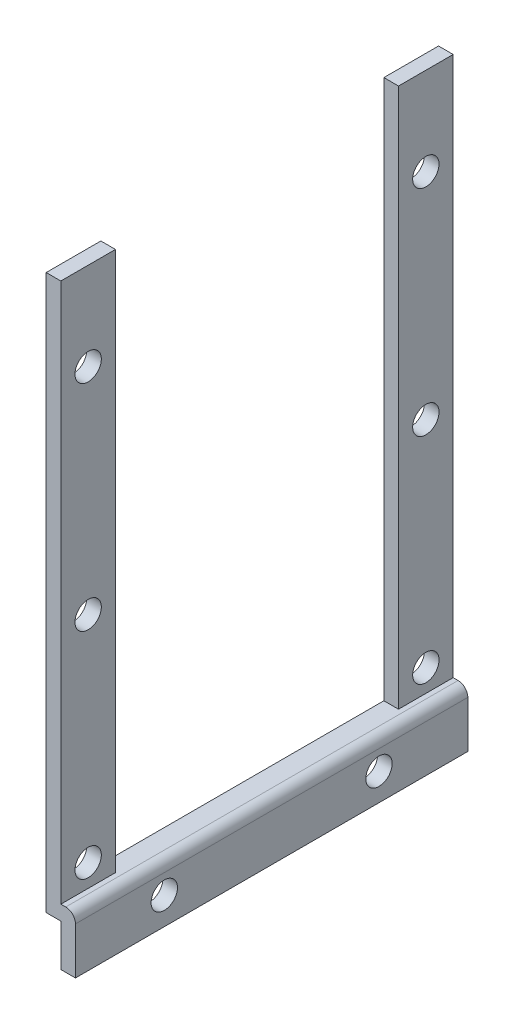
SolidWorks part; units mm, degrees
material "ABS"
ref_plane "Front Plane" through (0, 0, 0) normal (0, 0, 1) x (1, 0, 0)
ref_plane "Top Plane" through (0, 0, 0) normal (0, 1, 0) x (1, 0, 0)
ref_plane "Right Plane" through (0, 0, 0) normal (1, 0, 0) x (0, 0, -1)
sketch "Sketch1" plane through (0, 0, 0) normal (0, 0, 1) x (1, 0, 0)
  line L0 (0, 0) -> (0, 4.3)
  line L1 (0, 4.3) -> (-1.5, 4.3)
  line L2 (-1.5, 4.3) -> (-1.5, 61.1)
  line L3 (-1.5, 61.1) -> (0, 61.1)
  line L4 (0, 61.1) -> (0, 5.8)
  line L5 (0, 5.8) -> (1.5, 5.8)
  line L6 (1.5, 5.8) -> (1.5, 0)
  line L7 (1.5, 0) -> (0, 0)
  dimension "D1" = 1.5
  dimension "D2" = 1.5
  dimension "D3" = 1.5
  dimension "D4" = 61.1
  dimension "D5" = 4.3
  dimension "D6" = 1.5
extrude "Boss-Extrude1" add sketch "Sketch1" against normal blind 40.2
sketch "Sketch3" plane through (0, 0, 0) normal (1, 0, 0) x (0, 0, -1)
  line L0 (40.2, 61.1) -> (0, 61.1) construction
  line L1 (5.6, 61.1) -> (34.6, 61.1)
  line L2 (5.6, 61.1) -> (5.6, 5.8)
  line L3 (5.6, 5.8) -> (34.6, 5.8)
  line L4 (34.6, 61.1) -> (34.6, 5.8)
  line L5 (20.1, 0) -> (20.1, 61.1) construction
  line L6 (40.2, 0) -> (0, 0) construction
  line L7 (0, 8.1) -> (40.2, 8.1) construction
  line L8 (0, 5.8) -> (0, 61.1) construction
  line L9 (40.2, 5.8) -> (40.2, 61.1) construction
  line L10 (2.8, 43.1605) -> (2.8, -7.4395) construction
  line L11 (37.4, 50.6) -> (37.4, 0) construction
  line L12 (40.2, 5.8) -> (0, 5.8) construction
  circle A0 centre (2.8, 8.1) radius 1.35
  circle A1 centre (37.4, 8.1) radius 1.35
  circle A2 centre (2.8, 30.1) radius 1.35
  circle A3 centre (37.4, 30.1) radius 1.35
  circle A4 centre (2.8, 52.1) radius 1.35
  circle A5 centre (37.4, 52.1) radius 1.35
  dimension "D5" = 2.7
  dimension "D6" = 2.7
  dimension "D7" = 22
  dimension "D8" = 2.7
  dimension "D9" = 2.7
  dimension "D11" = 2.7
  dimension "D12" = 2.7
  dimension "D2" = 29
  dimension "D3" = 53
  dimension "D4" = 34.6
  dimension "D10" = 22
extrude "Cut-Extrude2" cut sketch "Sketch3" against normal up to next
fillet "Fillet1" radius 1 1 edges at (1.5, 5.8, -20.1)
sketch "Sketch4" plane through (1.5, 0, 0) normal (1, 0, 0) x (0, 0, -1)
  line L0 (0, 2.8) -> (40.2, 2.8) construction
  line L1 (0, 0) -> (0, 4.8) construction
  line L2 (40.2, 0) -> (40.2, 4.8) construction
  line L3 (40.2, 0) -> (0, 0) construction
  line L4 (20.1, 4.8) -> (20.1, 0) construction
  line L5 (40.2, 4.8) -> (0, 4.8) construction
  circle A0 centre (9.1, 2.8) radius 1.35
  circle A1 centre (31.1, 2.8) radius 1.35
  dimension "D1" = 2.7
  dimension "D2" = 2.7
  dimension "D3" = 2.8
  dimension "D4" = 22
extrude "Cut-Extrude3" cut sketch "Sketch4" against normal up to next
